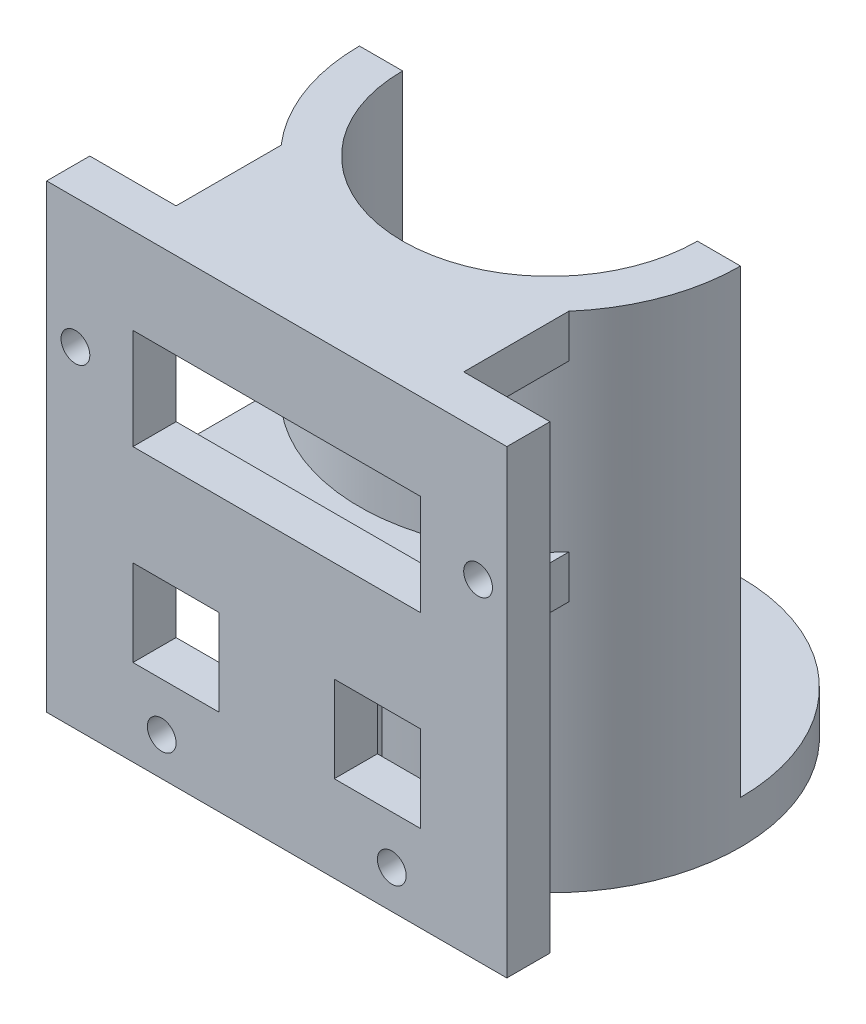
SolidWorks part; units mm, degrees
ref_plane "Front Plane" through (0, 0, 0) normal (0, 0, 1) x (1, 0, 0)
ref_plane "Top Plane" through (0, 0, 0) normal (0, 1, 0) x (1, 0, 0)
ref_plane "Right Plane" through (0, 0, 0) normal (1, 0, 0) x (0, 0, -1)
sketch "Sketch1" plane through (0, 0, 0) normal (0, 0, 1) x (1, 0, 0)
  line L0 (12.0803, 16) -> (12.0803, -16) construction
  line L1 (-16, -16) -> (16, -16)
  line L2 (-16, -16) -> (-16, 16)
  line L3 (-16, 16) -> (16, 16)
  line L4 (16, -16) -> (16, 16)
  line L5 (-16, -16) -> (16, 16) construction
  line L6 (-16, 16) -> (16, -16) construction
  line L7 (0, 0) -> (0, -20.1847) construction
  line L8 (-10, 3) -> (10, 3)
  line L9 (-10, 3) -> (-10, 10)
  line L10 (-10, 10) -> (10, 10)
  line L11 (10, 3) -> (10, 10)
  line L12 (-10, 3) -> (10, 10) construction
  line L13 (-10, 10) -> (10, 3) construction
  line L14 (-10, -4) -> (-4, -4)
  line L15 (-10, -4) -> (-10, -10)
  line L16 (-10, -10) -> (-4, -10)
  line L17 (-4, -4) -> (-4, -10)
  line L18 (10, -10) -> (4, -10)
  line L19 (4, -4) -> (4, -10)
  line L20 (10, -4) -> (10, -10)
  line L21 (10, -4) -> (4, -4)
  circle A0 centre (14, 7) radius 1
  circle A1 centre (-14, 7) radius 1
  circle A2 centre (-8, -13.3479) radius 1
  circle A3 centre (8, -13.3479) radius 1
  point P0 (0, 0)
  point P8 (0, 6.5)
  dimension "D9" = 2
  dimension "D13" = 2
  dimension "D1" = 32
  dimension "D2" = 32
  dimension "D3" = 6
  dimension "D4" = 20
  dimension "D5" = 7
  dimension "D6" = 6
  dimension "D7" = 6
  dimension "D8" = 7
  dimension "D10" = 2
  dimension "D11" = 9
  dimension "D12" = 8
  dimension "D14" = 3.3479
extrude "Boss-Extrude1" add sketch "Sketch1" along normal blind 3
sketch "Sketch2" plane through (0, -16, 0) normal (0, -1, 0) x (1, 0, 0)
  line L0 (0, -16) -> (4.1716, -16) construction
  line L1 (0, -16) -> (0, -13.1393) construction
  circle A0 centre (0, -16) radius 13.25
  circle A1 centre (-8, -16) radius 1
  circle A2 centre (0, -8) radius 1
  circle A3 centre (8, -16) radius 1
  circle A4 centre (0, -24) radius 1
  point P10 (0, -16)
  point P11 (0, 0)
  point P12 (0, 0)
  point P14 (0, 0)
  point P15 (0, -17.4303)
  point P16 (0, 0)
  point P17 (0, -16.9142)
  point P18 (0, 0)
  dimension "D1" = 2
  dimension "D2" = 8
  dimension "D3" = 8
  dimension "D4" = 16
extrude "Boss-Extrude2" add sketch "Sketch2" along normal blind 3 separate body
sketch "Sketch3" plane through (0, -16, 0) normal (0, 1, 0) x (1, 0, 0)
  line L0 (-13.25, 16) -> (-10.25, 16)
  line L1 (10.25, 16) -> (13.25, 16)
  arc A0 (-10.25, 16) -> (10.25, 16) centre (0, 16) ccw
  circle A1 centre (0, 16) radius 13.25
  arc A2 (-13.25, 16) -> (13.25, 16) centre (0, 16) ccw
  dimension "D2" = 3
  dimension "D1" = 0
extrude "Boss-Extrude3" add sketch "Sketch3" along normal up to vertex (32 mm away)
sketch "Sketch4" plane through (0, 0, 0) normal (0, 0, -1) x (-1, 0, 0)
  line L0 (-10, 3) -> (-10, 10) construction
  line L1 (10, 16) -> (-10, 16)
  line L2 (10, 16) -> (10, 13)
  line L3 (10, 13) -> (-10, 13)
  line L4 (-10, 16) -> (-10, 13)
  line L5 (10, 10) -> (10, 3) construction
  line L6 (10, 1.5) -> (-10, 1.5)
  line L7 (10, 1.5) -> (10, -1.5)
  line L8 (10, -1.5) -> (1.5, -1.5)
  line L9 (-10, 1.5) -> (-10, -1.5)
  line L10 (-16, 16) -> (16, 16) construction
  line L11 (10, 3) -> (-10, 3) construction
  line L12 (16, -16) -> (-16, -16) construction
  line L14 (1.5, -1.5) -> (1.5, -16)
  line L15 (1.5, -16) -> (-1.5, -16)
  line L16 (-1.5, -1.5) -> (-1.5, -16)
  line L17 (0, -1.5) -> (0, -16) construction
  line L18 (-1.5, -1.5) -> (-10, -1.5)
  dimension "D1" = 3
  dimension "D2" = 3
  dimension "D3" = 1.5
  dimension "D4" = 3
extrude "Boss-Extrude4" add sketch "Sketch4" along normal up to next
sketch "Sketch6" plane through (0, 0, 3) normal (0, 0, 1) x (1, 0, 0)
  circle A0 centre (8, -13.3479) radius 1 construction
  circle A1 centre (-8, -13.3479) radius 1 construction
  circle A2 centre (8, -13.3479) radius 1
  circle A3 centre (-8, -13.3479) radius 1
extrude "Cut-Extrude1" cut sketch "Sketch6" against normal through all
